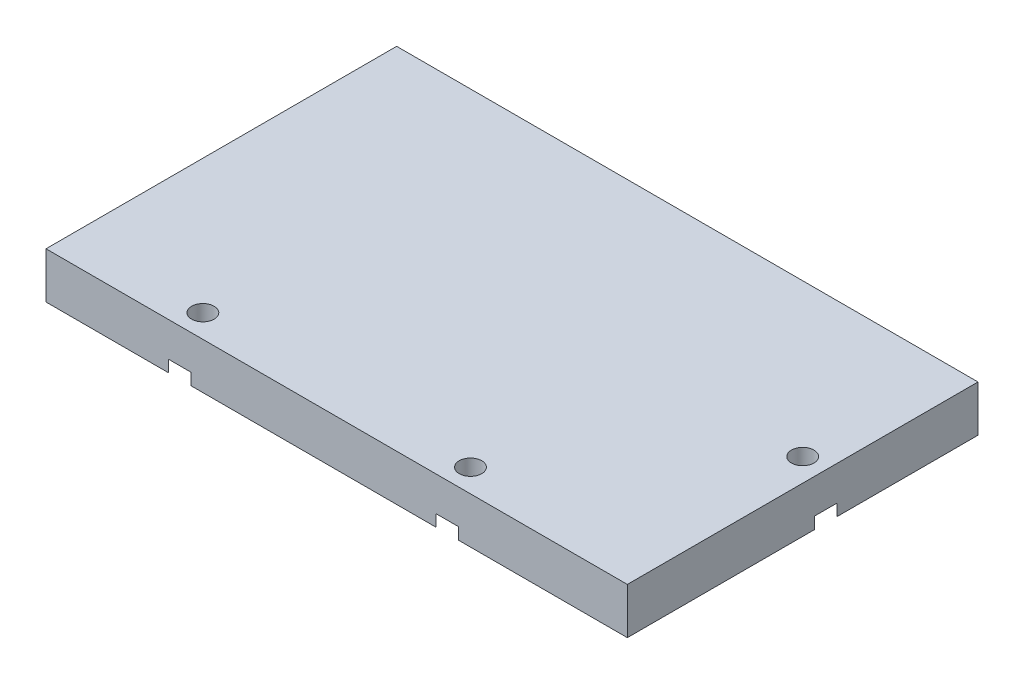
SolidWorks part; units mm, degrees
ref_plane "Front Plane" through (0, 0, 0) normal (0, 0, 1) x (1, 0, 0)
ref_plane "Top Plane" through (0, 0, 0) normal (0, 1, 0) x (1, 0, 0)
ref_plane "Right Plane" through (0, 0, 0) normal (1, 0, 0) x (0, 0, -1)
sketch "Sketch1" plane through (0, 0, 0) normal (0, 1, 0) x (1, 0, 0)
  line L1 (-31.5, 19) -> (31.5, 19)
  line L2 (-31.5, 19) -> (-31.5, -19)
  line L3 (-31.5, -19) -> (31.5, -19)
  line L4 (31.5, 19) -> (31.5, -19)
extrude "Boss-Extrude1" add sketch "Sketch1" along normal blind 5
sketch "Sketch4" plane through (0, 0, 0) normal (0, -1, 0) x (-1, 0, 0)
  line L0 (-31.5, 19) -> (-26.5, 19)
  line L1 (-31.5, 19) -> (31.5, 19) construction
  line L2 (-31.5, -19) -> (-26.5, -19)
  line L3 (31.5, -19) -> (-31.5, -19) construction
  line L4 (-26.5, -19) -> (-26.5, 19)
  line L5 (-31.5, -19) -> (-31.5, -14)
  line L6 (-31.5, -19) -> (-31.5, 19) construction
  line L7 (-31.5, -14) -> (-26.5, -14)
  line L8 (-31.5, 19) -> (-26.5, -14)
  line L9 (-31.5, -14) -> (-26.5, 19)
hole_wizard "CBORE for #2 Binding Head Machine Screw2" positions "Sketch8" profile "Sketch9" counterbore size "#2" standard "ANSI Inch" end condition through all
sketch "Sketch8" plane through (0, 0, 0) normal (0, -1, 0) x (-1, 0, 0)
  line L0 (-31.5, 19) -> (-26.5, -14) construction
  point P0 (-29, 2.5)
sketch "Sketch9" plane through (29, 0, -2.5) normal (1, 0, 0) x (0, 0, -1)
  line L0 (0, 0) -> (0, 5)
  line L1 (0, 5) -> (1.2192, 5)
  line L3 (1.2192, 5) -> (1.2192, 1.27)
  line L4 (1.2192, 1.27) -> (2.7788, 1.27)
  line L5 (2.7788, 1.27) -> (2.7788, 0)
  line L7 (2.7788, 0) -> (0, 0)
  line L11 (0, -6.35) -> (0, 107.95) construction
  dimension "Thru Hole Dia." = 2.4384
  dimension "Thru Hole Depth" = 5
  dimension "C'Bore Dia." = 5.5575
  dimension "C'Bore Depth" = 1.27
sketch "Sketch10" plane through (0, 0, 0) normal (0, -1, 0) x (-1, 0, 0)
  line L0 (-26.5, -14) -> (31.5, -14)
  line L1 (31.5, 19) -> (31.5, -19) construction
  line L2 (31.5, -14) -> (-26.5, -19)
  line L3 (31.5, -19) -> (-26.5, -14)
  line L4 (2.5, -16.5) -> (2.5, -19)
  line L5 (31.5, -19) -> (-31.5, -19) construction
  line L6 (2.5, -16.5) -> (2.5, -14)
  line L7 (31.5, -19) -> (2.5, -14)
  line L8 (2.5, -19) -> (31.5, -14)
  line L9 (2.5, -19) -> (-26.5, -14)
  line L10 (2.5, -14) -> (-26.5, -19)
hole_wizard "CBORE for #2 Binding Head Machine Screw3" positions "Sketch11" profile "Sketch12" counterbore size "#2" standard "ANSI Inch" end condition through all
sketch "Sketch11" plane through (0, 0, 0) normal (0, -1, 0) x (-1, 0, 0)
  line L0 (2.5, -19) -> (-26.5, -14) construction
  line L1 (31.5, -19) -> (2.5, -14) construction
  point P0 (-12, -16.5)
  point P4 (17, -16.5)
sketch "Sketch12" plane through (12, 0, 16.5) normal (1, 0, 0) x (0, 0, -1)
  line L0 (0, 0) -> (0, 5)
  line L1 (0, 5) -> (1.2192, 5)
  line L3 (1.2192, 5) -> (1.2192, 1.27)
  line L4 (1.2192, 1.27) -> (2.7788, 1.27)
  line L5 (2.7788, 1.27) -> (2.7788, 0)
  line L7 (2.7788, 0) -> (0, 0)
  line L11 (0, -6.35) -> (0, 107.95) construction
  dimension "Thru Hole Dia." = 2.4384
  dimension "Thru Hole Depth" = 5
  dimension "C'Bore Dia." = 5.5575
  dimension "C'Bore Depth" = 1.27
sketch "Sketch13" plane through (0, 0, -19) normal (0, 0, -1) x (-1, 0, 0)
  line L0 (-26.2212, 0) -> (-26.2212, 5)
  line L1 (-31.5, 5) -> (31.5, 5) construction
  line L2 (-26.2212, 5) -> (31.5, 0)
  line L3 (31.5, 0) -> (31.5, 5)
  line L4 (31.5, 5) -> (-26.2212, 0)
  line L5 (2.6394, 2.5) -> (2.6394, 0)
  line L8 (2.5, 0) -> (31.5, 0) construction
  line L9 (2.6394, 2.5) -> (2.6394, 5)
  line L10 (-26.2212, 5) -> (2.6394, 0)
  line L11 (2.6394, 0) -> (31.5, 5)
  line L12 (-26.2212, 0) -> (2.6394, 5)
  line L13 (2.6394, 5) -> (31.5, 0)
hole_wizard "#2-56 Tapped Hole1" positions "Sketch14" profile "Sketch15" tap size "#2-56" standard "ANSI Inch"
sketch "Sketch14" plane through (0, 0, -19) normal (0, 0, -1) x (-1, 0, 0)
  line L0 (-26.2212, 5) -> (2.6394, 0) construction
  line L1 (2.6394, 0) -> (31.5, 5) construction
  point P0 (-11.7909, 2.5)
  point P4 (17.0697, 2.5)
sketch "Sketch15" plane through (11.7909, 2.5, -19) normal (1, 0, 0) x (0, 1, 0)
  line L0 (0, 0) -> (0, 10)
  line L1 (0, 10) -> (0.889, 9.4658)
  line L2 (0.889, 9.4658) -> (0.889, 0)
  line L5 (0.889, 0) -> (0, 0)
  line L10 (0, 10) -> (-0.889, 9.4658) construction
  line L11 (0, -6.35) -> (0, 107.95) construction
  dimension "Tap Drill Dia." = 1.778
  dimension "Tap Drill Depth" = 10
  dimension "Drill Angle" = 118
cosmetic thread "Hole Thread1" parameters "D1"=10, "D2"=2.1844
cosmetic thread "Hole Thread2" parameters "D1"=10, "D2"=2.1844
